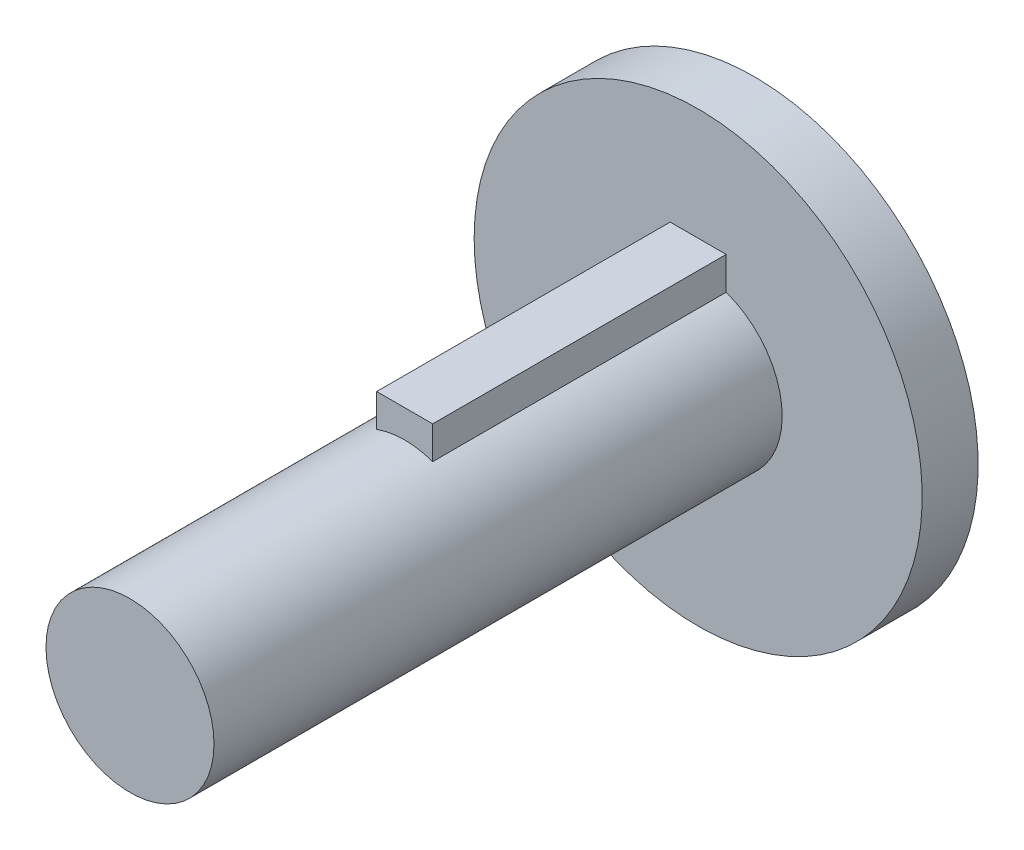
SolidWorks part; units mm, degrees
ref_plane "Front Plane" through (0, 0, 0) normal (0, 0, 1) x (1, 0, 0)
ref_plane "Top Plane" through (0, 0, 0) normal (0, 1, 0) x (1, 0, 0)
ref_plane "Right Plane" through (0, 0, 0) normal (1, 0, 0) x (0, 0, -1)
sketch "Sketch1" plane through (0, 0, 0) normal (0, 0, 1) x (1, 0, 0)
  circle A0 centre (0, 0) radius 3
  dimension "D1" = 6
extrude "Boss-Extrude1" add sketch "Sketch1" along normal blind 20.29
sketch "Sketch2" plane through (0, 0, 0) normal (0, 0, -1) x (-1, 0, 0)
  line L0 (-1, 2.8284) -> (-1, 3.9984)
  line L1 (-1, 3.9984) -> (1, 3.9984)
  line L2 (1, 3.9984) -> (1, 2.8284)
  line L3 (-1, 2.8284) -> (1, 2.8284)
  circle A0 centre (0, 0) radius 3 construction
  point P4 (0, 3.9984)
  dimension "D1" = 1.17
  dimension "D2" = 2
extrude "Boss-Extrude2" add sketch "Sketch2" against normal blind 10.48
sketch "Sketch3" plane through (0, 0, 0) normal (0, 0, -1) x (-1, 0, 0)
  circle A0 centre (0, 0) radius 8
extrude "Boss-Extrude3" add sketch "Sketch3" along normal blind 2
